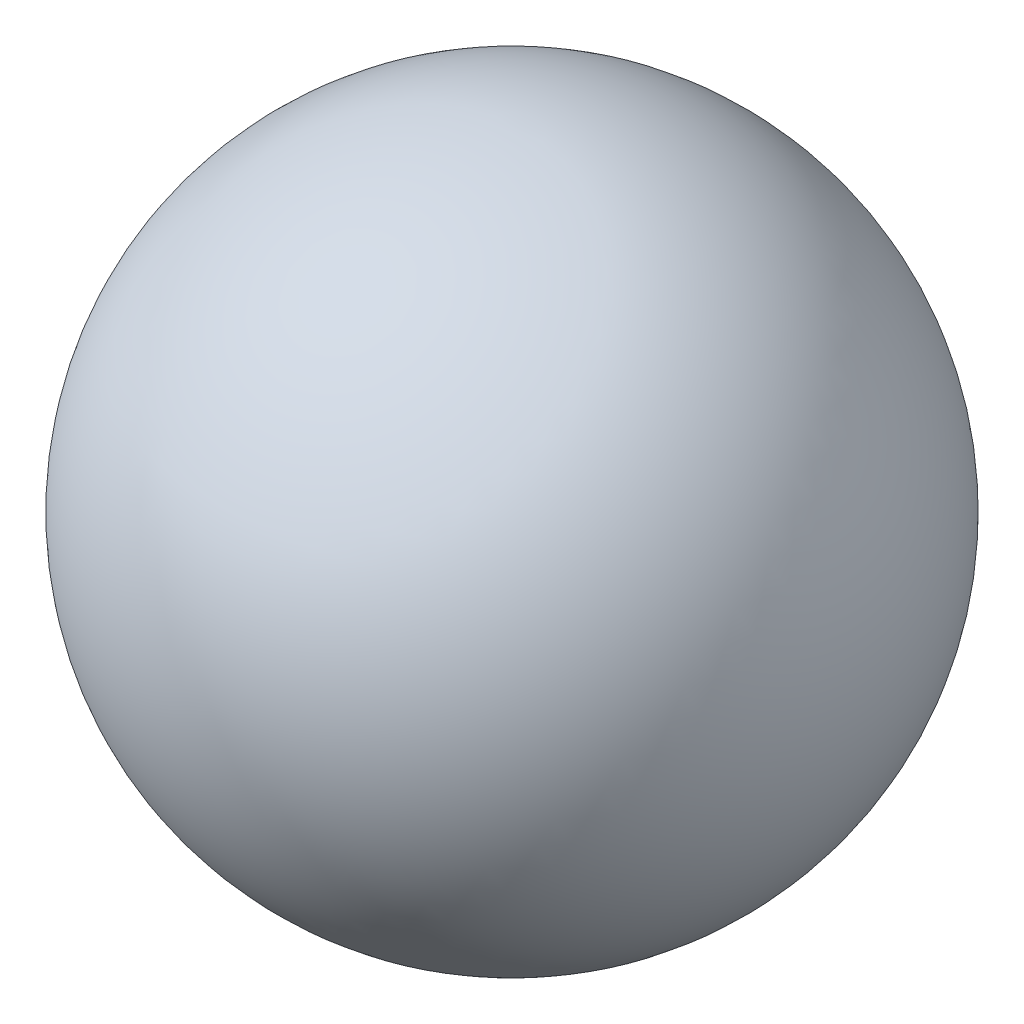
SolidWorks part; units mm, degrees
ref_plane "Front Plane" through (0, 0, 0) normal (0, 0, 1) x (1, 0, 0)
ref_plane "Top Plane" through (0, 0, 0) normal (0, 1, 0) x (1, 0, 0)
ref_plane "Right Plane" through (0, 0, 0) normal (1, 0, 0) x (0, 0, -1)
sketch "Szkic1" plane through (0, 0, 0) normal (0, 0, 1) x (1, 0, 0)
  line L0 (0, 0) -> (0, 100) construction
  line L1 (0, 0) -> (0, 100)
  arc A1 (0, 0) -> (0, 100) centre (0, 50) ccw
  point P3 (0, 0)
  dimension "D1" = 100
revolve "Obrót4" add sketch "Szkic1" angle 360 about L0
